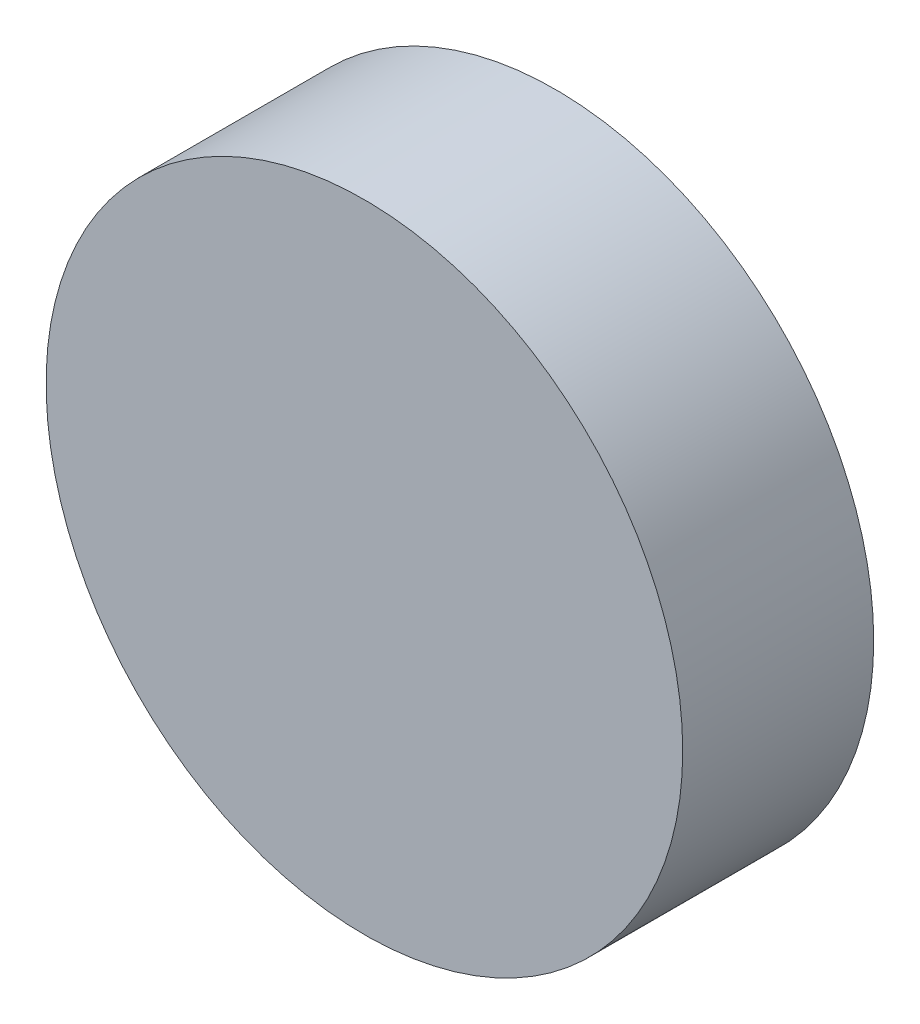
SolidWorks part; units mm, degrees
ref_plane "Front Plane" through (0, 0, 0) normal (0, 0, 1) x (1, 0, 0)
ref_plane "Top Plane" through (0, 0, 0) normal (0, 1, 0) x (1, 0, 0)
ref_plane "Right Plane" through (0, 0, 0) normal (1, 0, 0) x (0, 0, -1)
sketch "Sketch1" plane through (0, 0, 0) normal (0, 0, 1) x (1, 0, 0)
  circle A0 centre (0, 0) radius 2.5
  dimension "D1" = 5
extrude "Boss-Extrude1" add sketch "Sketch1" along normal blind 1.5
